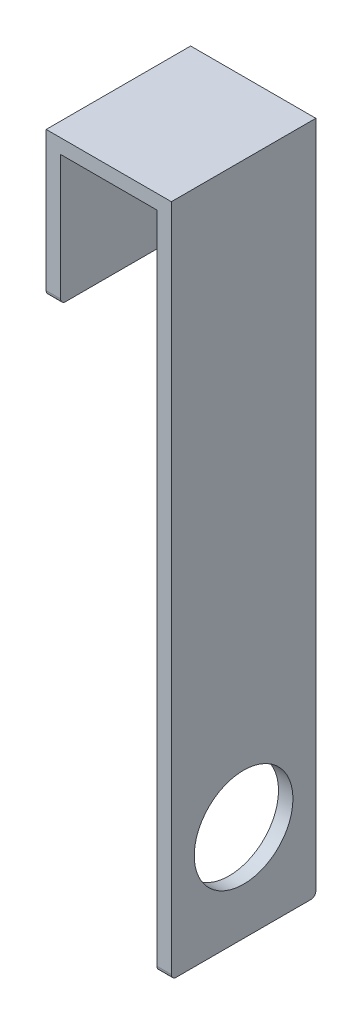
SolidWorks part; units mm, degrees
ref_plane "Спереди" through (0, 0, 0) normal (0, 0, 1) x (1, 0, 0)
ref_plane "Сверху" through (0, 0, 0) normal (0, 1, 0) x (1, 0, 0)
ref_plane "Справа" through (0, 0, 0) normal (1, 0, 0) x (0, 0, -1)
sketch "Эскиз1" plane through (0, 0, 0) normal (0, 0, 1) x (1, 0, 0)
  line L0 (0, 75.5907) -> (0, -113.0068) construction
  line L1 (-20, 7.0298) -> (-20, 34.0298)
  line L2 (-20, 34.0298) -> (0, 34.0298)
  line L3 (0, 34.0298) -> (0, -102.9702)
  line L4 (0, -102.9702) -> (3, -102.9702)
  line L5 (3, -102.9702) -> (3, 37.0298)
  line L6 (3, 37.0298) -> (-23, 37.0298)
  line L7 (-23, 37.0298) -> (-23, 7.0298)
  line L8 (-23, 7.0298) -> (-20, 7.0298)
  dimension "D1" = 140
  dimension "D2" = 3
  dimension "D3" = 20
  dimension "D4" = 3
  dimension "D5" = 3
  dimension "D6" = 30
extrude "Бобышка-Вытянуть1" add sketch "Эскиз1" along normal blind 30 contours L1 L2 L3 L4 L5 L6 L7 L8
sketch "Эскиз2" plane through (3, 0, 0) normal (1, 0, 0) x (0, 0, -1)
  line L0 (-15, -102.9702) -> (-15, 63.8603) construction
  line L1 (-30, -102.9702) -> (0, -102.9702) construction
  line L2 (-43.6532, -52.9702) -> (13.6532, -52.9702) construction
  line L3 (-30, 37.0298) -> (0, 37.0298) construction
  circle A0 centre (-15, -82.9702) radius 10.25
  point P6 (-15, -52.9702)
  dimension "D2" = 20.5
  dimension "D1" = 90
  dimension "D3" = 20
extrude "Вырез-Вытянуть1" cut sketch "Эскиз2" against normal blind 30
fillet "Скругление2" radius 1 1 edges at (1.5, -102.9702, 30)
fillet "Скругление3" radius 1 1 edges at (1.5, -102.9702, 0)
fillet "Скругление4" radius 1 1 edges at (-21.5, 7.0298, 30)
fillet "Скругление5" radius 1 1 edges at (-21.5, 7.0298, 0)
